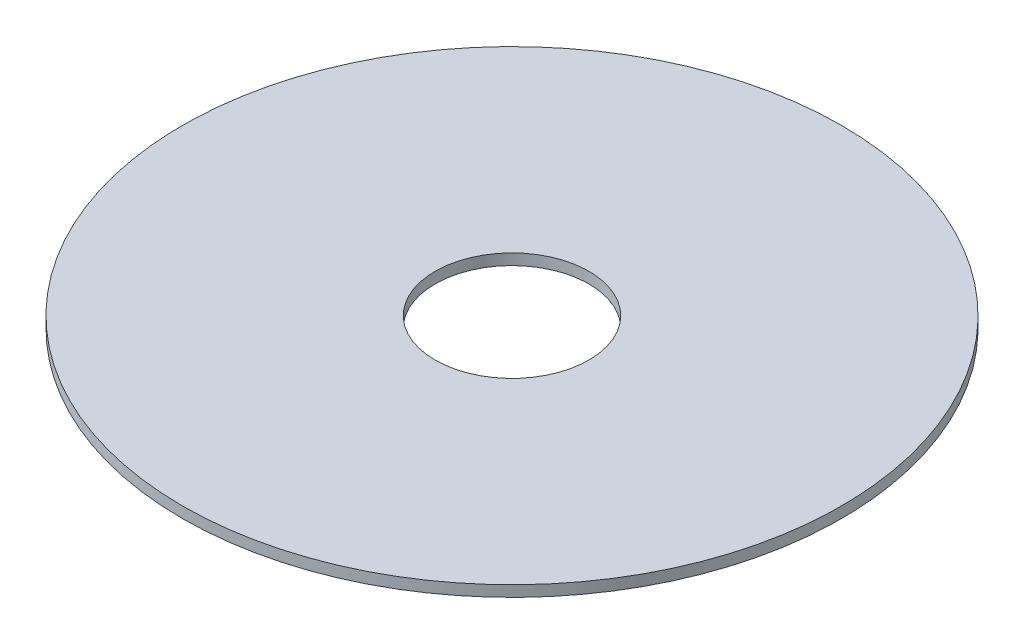
SolidWorks part; units mm, degrees
ref_plane "Front" through (0, 0, 0) normal (0, 0, 1) x (1, 0, 0)
ref_plane "Top" through (0, 0, 0) normal (0, 1, 0) x (1, 0, 0)
ref_plane "Right" through (0, 0, 0) normal (1, 0, 0) x (0, 0, -1)
sketch "Sketch1" plane through (0, 0, 0) normal (0, 1, 0) x (1, 0, 0)
  circle A0 centre (0, 0) radius 15
  circle A1 centre (0, 0) radius 3.5
  dimension "D1" = 30
  dimension "D2" = 7
extrude "Boss-Extrude1" add sketch "Sketch1" along normal blind 0.5
